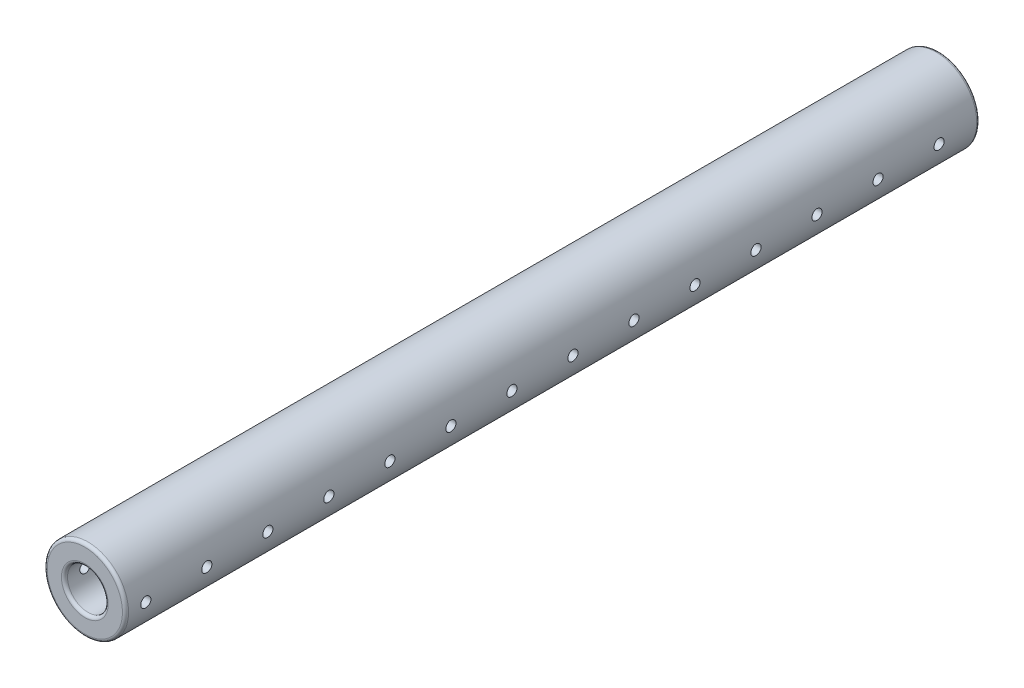
SolidWorks part; units mm, degrees
ref_plane "Front Plane" through (0, 0, 0) normal (0, 0, 1) x (1, 0, 0)
ref_plane "Top Plane" through (0, 0, 0) normal (0, 1, 0) x (1, 0, 0)
ref_plane "Right Plane" through (0, 0, 0) normal (1, 0, 0) x (0, 0, -1)
sketch "Sketch1" plane through (0, 0, 0) normal (0, 0, 1) x (1, 0, 0)
  circle A0 centre (0, 0) radius 10
  circle A1 centre (0, 0) radius 20
  dimension "D1" = 40
  dimension "D2" = 20
extrude "Boss-Extrude1" add sketch "Sketch1" along normal blind 420
sketch "Sketch2" plane through (0, 0, 0) normal (1, 0, 0) x (0, 0, -1)
  line L0 (0, -20) -> (0, 20) construction
  circle A0 centre (-20, 0) radius 2.5
  circle A1 centre (-50, 0) radius 2.5
  circle A2 centre (-80, 0) radius 2.5
  circle A3 centre (-110, 0) radius 2.5
  circle A4 centre (-140, 0) radius 2.5
  circle A5 centre (-170, 0) radius 2.5
  circle A6 centre (-200, 0) radius 2.5
  circle A7 centre (-230, 0) radius 2.5
  circle A8 centre (-260, 0) radius 2.5
  circle A9 centre (-290, 0) radius 2.5
  circle A10 centre (-320, 0) radius 2.5
  circle A11 centre (-350, 0) radius 2.5
  circle A12 centre (-380, 0) radius 2.5
  circle A13 centre (-410, 0) radius 2.5
  dimension "D1" = 5
  dimension "D4" = 30
  dimension "D2" = 20
  dimension "D3" = 14
extrude "Cut-Extrude1" cut sketch "Sketch2" against normal through all both and the other way through all
fillet "Fillet1" radius 1.5 4 edges at (10, 0, 0) (20, 0, 0) (10, 0, 420) (20, 0, 420)
